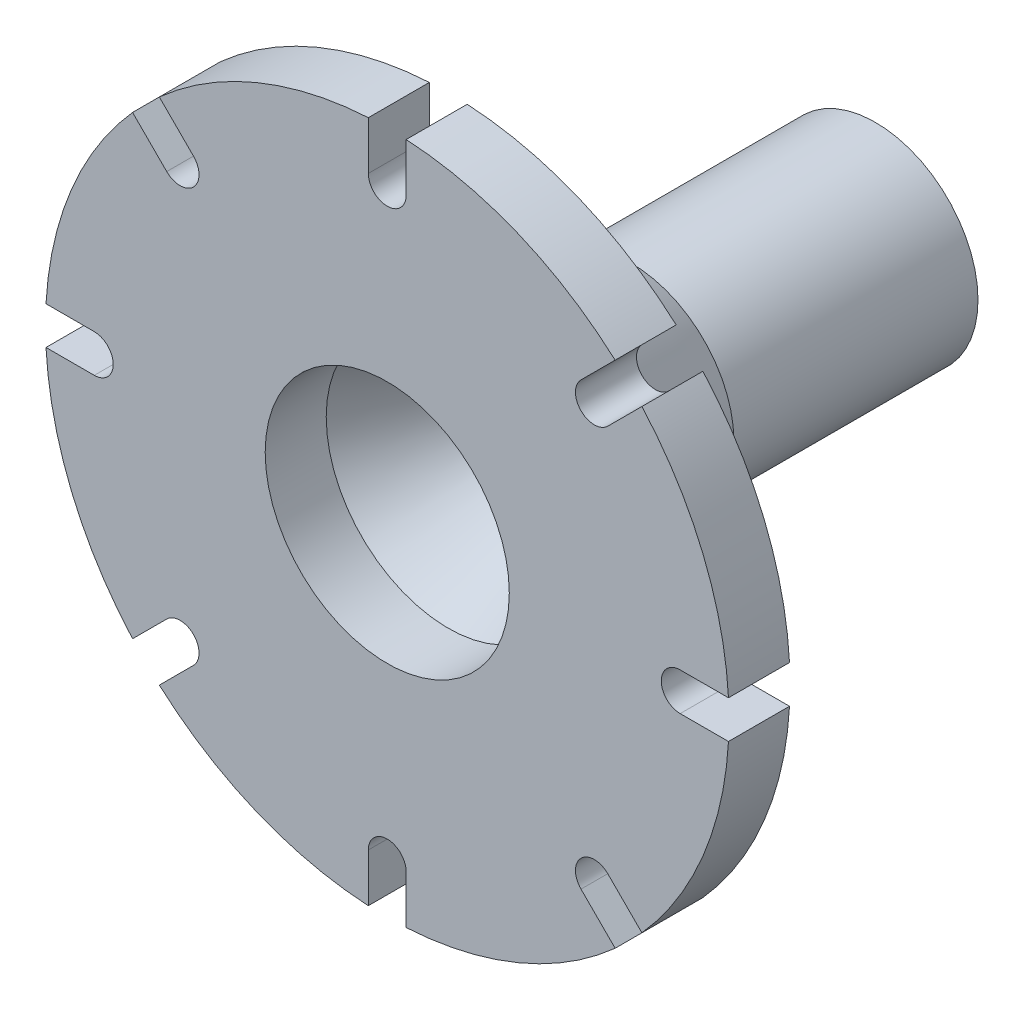
SolidWorks part; units mm, degrees
ref_plane "Front Plane" through (0, 0, 0) normal (0, 0, 1) x (1, 0, 0)
ref_plane "Top Plane" through (0, 0, 0) normal (0, 1, 0) x (1, 0, 0)
ref_plane "Right Plane" through (0, 0, 0) normal (1, 0, 0) x (0, 0, -1)
sketch "Sketch1" plane through (0, 0, 0) normal (0, 0, 1) x (1, 0, 0)
  circle A0 centre (0, 0) radius 3.4
  circle A1 centre (0, 0) radius 8.4
  dimension "D1" = 6.8
  dimension "D2" = 5
extrude "Boss-Extrude1" add sketch "Sketch1" along normal blind 20
sketch "Sketch2" plane through (0, 0, 20) normal (0, 0, 1) x (1, 0, 0)
  circle A0 centre (0, 0) radius 2.4
  circle A1 centre (0, 0) radius 8.4
  circle A2 centre (0, 0) radius 3.4 construction
  dimension "D1" = 1
extrude "Boss-Extrude2" add sketch "Sketch2" against normal blind 1.5
ref_plane "Plane1" through (0, 0, 35) normal (0, 0, 1) x (1, 0, 0)
sketch "Sketch3" plane through (0, 0, 35) normal (0, 0, 1) x (1, 0, 0)
  circle A0 centre (0, 0) radius 10
  circle A1 centre (0, 0) radius 15
  dimension "D1" = 30
  dimension "D2" = 5
extrude "Boss-Extrude3" add sketch "Sketch3" along normal blind 5 separate body
sketch "Sketch4" plane through (0, 0, 0) normal (0, 1, 0) x (1, 0, 0)
  line L0 (-8.4, -20) -> (-15, -35)
  line L1 (-15, -35) -> (-10, -35)
  line L2 (-10, -35) -> (-2.4, -20)
  line L3 (-2.4, -20) -> (-8.4, -20)
  line L4 (0, -20) -> (0, -35) construction
  line L5 (-8.4, -20) -> (8.4, -20) construction
  line L6 (-55, -35) -> (55, -35) construction
revolve "Revolve1" add sketch "Sketch4" angle 360 about L4
sketch "Sketch5" plane through (0, 0, 40) normal (0, 0, 1) x (1, 0, 0)
  circle A0 centre (0, 0) radius 10
  circle A1 centre (0, 0) radius 28
  circle A2 centre (0, 0) radius 10 construction
  dimension "D1" = 18
extrude "Boss-Extrude4" add sketch "Sketch5" against normal blind 5
sketch "Sketch6" plane through (0, 0, 35) normal (0, 0, -1) x (-1, 0, 0)
  line L0 (0, 20) -> (0, 28) construction
  line L1 (-1.55, 24) -> (-1.55, 29)
  line L2 (-1.55, 29) -> (1.55, 29)
  line L3 (1.55, 29) -> (1.55, 24)
  line L4 (21.6021, 19.4101) -> (18.0666, 15.8745)
  line L5 (19.4101, 21.6021) -> (21.6021, 19.4101)
  line L6 (15.8745, 18.0666) -> (19.4101, 21.6021)
  line L7 (29, -1.55) -> (24, -1.55)
  line L8 (29, 1.55) -> (29, -1.55)
  line L9 (24, 1.55) -> (29, 1.55)
  line L10 (19.4101, -21.6021) -> (15.8745, -18.0666)
  line L11 (21.6021, -19.4101) -> (19.4101, -21.6021)
  line L12 (18.0666, -15.8745) -> (21.6021, -19.4101)
  line L13 (-1.55, -29) -> (-1.55, -24)
  line L14 (1.55, -29) -> (-1.55, -29)
  line L15 (1.55, -24) -> (1.55, -29)
  line L16 (-21.6021, -19.4101) -> (-18.0666, -15.8745)
  line L17 (-19.4101, -21.6021) -> (-21.6021, -19.4101)
  line L18 (-15.8745, -18.0666) -> (-19.4101, -21.6021)
  line L19 (-29, 1.55) -> (-24, 1.55)
  line L20 (-29, -1.55) -> (-29, 1.55)
  line L21 (-24, -1.55) -> (-29, -1.55)
  line L22 (-19.4101, 21.6021) -> (-15.8745, 18.0666)
  line L23 (-21.6021, 19.4101) -> (-19.4101, 21.6021)
  line L24 (-18.0666, 15.8745) -> (-21.6021, 19.4101)
  arc A0 (-1.55, 24) -> (1.55, 24) centre (0, 24) ccw
  circle A2 centre (0, 0) radius 28 construction
  arc A3 (15.8745, 18.0666) -> (18.0666, 15.8745) centre (16.9706, 16.9706) ccw
  arc A4 (24, 1.55) -> (24, -1.55) centre (24, 0) ccw
  arc A5 (18.0666, -15.8745) -> (15.8745, -18.0666) centre (16.9706, -16.9706) ccw
  arc A6 (1.55, -24) -> (-1.55, -24) centre (0, -24) ccw
  arc A7 (-15.8745, -18.0666) -> (-18.0666, -15.8745) centre (-16.9706, -16.9706) ccw
  arc A8 (-24, -1.55) -> (-24, 1.55) centre (-24, 0) ccw
  arc A9 (-18.0666, 15.8745) -> (-15.8745, 18.0666) centre (-16.9706, 16.9706) ccw
  point P4 (0, 20)
  point P10 (0, 24)
  point P14 (-22.4283, 16.7622)
  point P15 (0, 0)
  point P50 (0, 0)
  point P52 (0, 0)
  point P53 (0, 0)
  point P54 (-7.5918, 10.7503)
  point P55 (0, 0)
  point P56 (-7.2867, 7.1233)
  point P57 (0, 0)
  point P59 (-2.6507, -6.3974)
  dimension "D1" = 3.1
  dimension "D3" = 1
  dimension "D4" = 8
  dimension "D2" = 8
extrude "Cut-Extrude1" cut sketch "Sketch6" against normal blind 5
sketch "Sketch7" plane through (0, 0, 40) normal (0, 0, 1) x (1, 0, 0)
  line L0 (9.5, 0) -> (12.9, 0) construction
  circle A0 centre (0, 0) radius 9.5
  circle A1 centre (0, 0) radius 12.9
  circle A2 centre (0, 0) radius 11.2 construction
  point P7 (11.2, 0)
  dimension "D1" = 19
  dimension "D2" = 3.4
